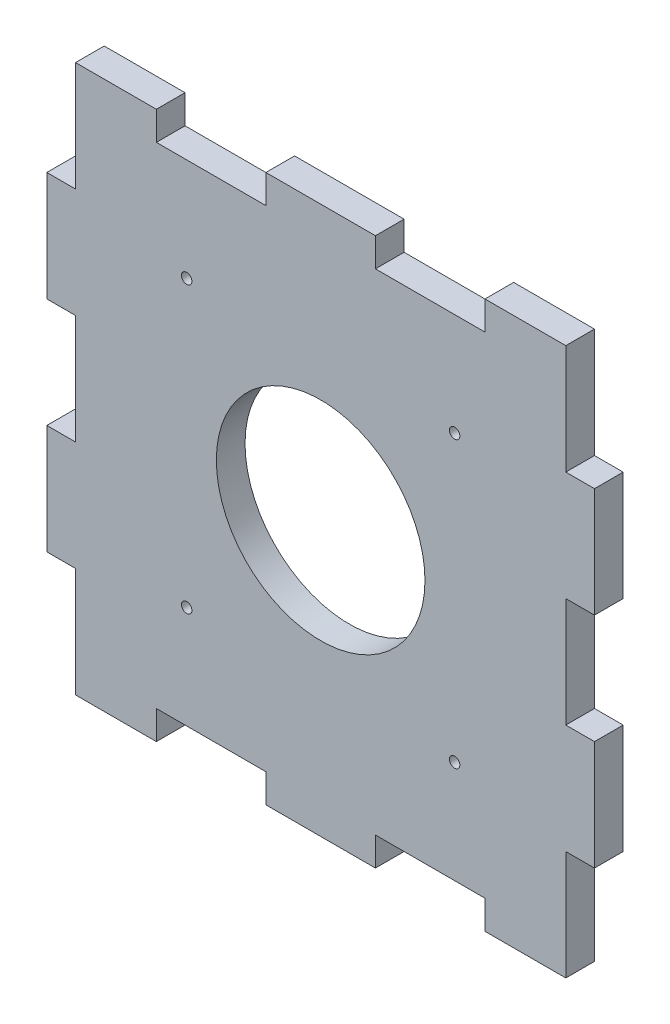
SolidWorks part; units mm, degrees
ref_plane "Alzado" through (0, 0, 0) normal (0, 0, 1) x (1, 0, 0)
ref_plane "Planta" through (0, 0, 0) normal (0, 1, 0) x (1, 0, 0)
ref_plane "Vista lateral" through (0, 0, 0) normal (1, 0, 0) x (0, 0, -1)
sketch "Croquis1" plane through (0, 0, 0) normal (0, 0, 1) x (1, 0, 0)
  line L0 (-47, 50) -> (-47, 31.5)
  line L1 (-47, 31.5) -> (-50, 31.5)
  line L2 (-50, 31.5) -> (-50, 10.5)
  line L3 (-50, 10.5) -> (-47, 10.5)
  line L4 (-47, 10.5) -> (-47, -10.5)
  line L5 (-47, -10.5) -> (-50, -10.5)
  line L6 (-50, -10.5) -> (-50, -31.5)
  line L7 (-50, -31.5) -> (-47, -31.5)
  line L8 (-47, -31.5) -> (-47, -50)
  line L9 (-47, -50) -> (-31.5, -50)
  line L10 (-31.5, -50) -> (-31.5, -47)
  line L11 (-31.5, -47) -> (-10.5, -47)
  line L12 (-10.5, -47) -> (-10.5, -50)
  line L13 (-10.5, -50) -> (10.5, -50)
  line L14 (10.5, -50) -> (10.5, -47)
  line L15 (10.5, -47) -> (31.5, -47)
  line L16 (31.5, -47) -> (31.5, -50)
  line L17 (31.5, -50) -> (47, -50)
  line L18 (47, -50) -> (47, -31.5)
  line L19 (47, -31.5) -> (50, -31.5)
  line L20 (50, -31.5) -> (50, -10.5)
  line L21 (50, -10.5) -> (47, -10.5)
  line L22 (47, -10.5) -> (47, 10.5)
  line L23 (47, 10.5) -> (50, 10.5)
  line L24 (50, 10.5) -> (50, 31.5)
  line L25 (50, 31.5) -> (47, 31.5)
  line L26 (47, 31.5) -> (47, 50)
  line L27 (47, 50) -> (31.5, 50)
  line L28 (31.5, 50) -> (31.5, 47)
  line L29 (31.5, 47) -> (10.5, 47)
  line L30 (10.5, 47) -> (10.5, 50)
  line L31 (10.5, 50) -> (-10.5, 50)
  line L32 (-10.5, 50) -> (-10.5, 47)
  line L33 (-10.5, 47) -> (-31.5, 47)
  line L34 (-31.5, 47) -> (-31.5, 50)
  line L35 (-31.5, 50) -> (-47, 50)
  line L36 (-47, 50) -> (47, -50) construction
  line L37 (-47, -50) -> (47, 50) construction
  line L38 (47, 0) -> (0, 0) construction
  line L39 (0, 0) -> (0, 5.738) construction
  line L40 (0, 50) -> (0, 0) construction
  circle A4 centre (0, 0) radius 20
  circle A5 centre (0, 0) radius 37.5 construction
  circle A7 centre (25.6841, 27.3235) radius 1
  circle A8 centre (25.6841, -27.3235) radius 1
  circle A9 centre (-25.6841, 27.3235) radius 1
  circle A10 centre (-25.6841, -27.3235) radius 1
  point P36 (0, 0)
  point P37 (-39.25, -50)
  point P51 (0, 0)
  dimension "D3" = 40
  dimension "D4" = 75
  dimension "D5" = 2
  dimension "D1" = 100
  dimension "D2" = 100
extrude "Saliente-Extruir1" add sketch "Croquis1" along normal blind 5.5
sketch "Croquis2" plane through (50, 0, 0) normal (1, 0, 0) x (0, 0, -1)
  line L0 (0, -31.5) -> (0, -10.5) construction
  line L1 (0, -10.5) -> (-5.5, -10.5) construction
  line L2 (-5.5, -10.5) -> (-5.5, -31.5) construction
  line L3 (-5.5, -31.5) -> (0, -31.5) construction
  line L4 (0, 10.5) -> (0, 31.5) construction
  line L5 (0, 31.5) -> (-5.5, 31.5) construction
  line L6 (-5.5, 31.5) -> (-5.5, 10.5) construction
  line L7 (-5.5, 10.5) -> (0, 10.5) construction
  line L8 (0, -31.5) -> (0, -10.5)
  line L9 (0, -10.5) -> (-5.5, -10.5)
  line L10 (-5.5, -10.5) -> (-5.5, -31.5)
  line L11 (-5.5, -31.5) -> (0, -31.5)
  line L12 (0, 10.5) -> (0, 31.5)
  line L13 (0, 31.5) -> (-5.5, 31.5)
  line L14 (-5.5, 31.5) -> (-5.5, 10.5)
  line L15 (-5.5, 10.5) -> (0, 10.5)
extrude "Saliente-Extruir2" add sketch "Croquis2" along normal blind 2.5
sketch "Croquis3" plane through (0, -50, 0) normal (0, -1, 0) x (1, 0, 0)
  line L0 (31.5, 0) -> (47, 0) construction
  line L1 (47, 0) -> (47, 5.5) construction
  line L2 (47, 5.5) -> (31.5, 5.5) construction
  line L3 (31.5, 5.5) -> (31.5, 0) construction
  line L4 (-10.5, 0) -> (10.5, 0) construction
  line L5 (10.5, 0) -> (10.5, 5.5) construction
  line L6 (10.5, 5.5) -> (-10.5, 5.5) construction
  line L7 (-10.5, 5.5) -> (-10.5, 0) construction
  line L8 (-47, 0) -> (-31.5, 0) construction
  line L9 (-31.5, 0) -> (-31.5, 5.5) construction
  line L10 (-31.5, 5.5) -> (-47, 5.5) construction
  line L11 (-47, 5.5) -> (-47, 0) construction
  line L12 (31.5, 0) -> (47, 0)
  line L13 (47, 0) -> (47, 5.5)
  line L14 (47, 5.5) -> (31.5, 5.5)
  line L15 (31.5, 5.5) -> (31.5, 0)
  line L16 (-10.5, 0) -> (10.5, 0)
  line L17 (10.5, 0) -> (10.5, 5.5)
  line L18 (10.5, 5.5) -> (-10.5, 5.5)
  line L19 (-10.5, 5.5) -> (-10.5, 0)
  line L20 (-47, 0) -> (-31.5, 0)
  line L21 (-31.5, 0) -> (-31.5, 5.5)
  line L22 (-31.5, 5.5) -> (-47, 5.5)
  line L23 (-47, 5.5) -> (-47, 0)
extrude "Saliente-Extruir3" add sketch "Croquis3" along normal blind 2.5
sketch "Croquis4" plane through (-50, 0, 0) normal (-1, 0, 0) x (0, 0, 1)
  line L0 (0, -10.5) -> (0, -31.5) construction
  line L1 (0, -31.5) -> (5.5, -31.5) construction
  line L2 (5.5, -31.5) -> (5.5, -10.5) construction
  line L3 (5.5, -10.5) -> (0, -10.5) construction
  line L4 (0, 31.5) -> (0, 10.5) construction
  line L5 (0, 10.5) -> (5.5, 10.5) construction
  line L6 (5.5, 10.5) -> (5.5, 31.5) construction
  line L7 (5.5, 31.5) -> (0, 31.5) construction
  line L8 (0, -10.5) -> (0, -31.5)
  line L9 (0, -31.5) -> (5.5, -31.5)
  line L10 (5.5, -31.5) -> (5.5, -10.5)
  line L11 (5.5, -10.5) -> (0, -10.5)
  line L12 (0, 31.5) -> (0, 10.5)
  line L13 (0, 10.5) -> (5.5, 10.5)
  line L14 (5.5, 10.5) -> (5.5, 31.5)
  line L15 (5.5, 31.5) -> (0, 31.5)
extrude "Saliente-Extruir4" add sketch "Croquis4" along normal blind 2.5
sketch "Croquis5" plane through (0, 50, 0) normal (0, 1, 0) x (1, 0, 0)
  line L0 (-31.5, 0) -> (-47, 0) construction
  line L1 (-47, 0) -> (-47, -5.5) construction
  line L2 (-47, -5.5) -> (-31.5, -5.5) construction
  line L3 (-31.5, -5.5) -> (-31.5, 0) construction
  line L4 (10.5, 0) -> (-10.5, 0) construction
  line L5 (-10.5, 0) -> (-10.5, -5.5) construction
  line L6 (-10.5, -5.5) -> (10.5, -5.5) construction
  line L7 (10.5, -5.5) -> (10.5, 0) construction
  line L8 (47, 0) -> (31.5, 0) construction
  line L9 (31.5, 0) -> (31.5, -5.5) construction
  line L10 (31.5, -5.5) -> (47, -5.5) construction
  line L11 (47, -5.5) -> (47, 0) construction
  line L12 (-31.5, 0) -> (-47, 0)
  line L13 (-47, 0) -> (-47, -5.5)
  line L14 (-47, -5.5) -> (-31.5, -5.5)
  line L15 (-31.5, -5.5) -> (-31.5, 0)
  line L16 (10.5, 0) -> (-10.5, 0)
  line L17 (-10.5, 0) -> (-10.5, -5.5)
  line L18 (-10.5, -5.5) -> (10.5, -5.5)
  line L19 (10.5, -5.5) -> (10.5, 0)
  line L20 (47, 0) -> (31.5, 0)
  line L21 (31.5, 0) -> (31.5, -5.5)
  line L22 (31.5, -5.5) -> (47, -5.5)
  line L23 (47, -5.5) -> (47, 0)
extrude "Saliente-Extruir5" add sketch "Croquis5" along normal blind 2.5
